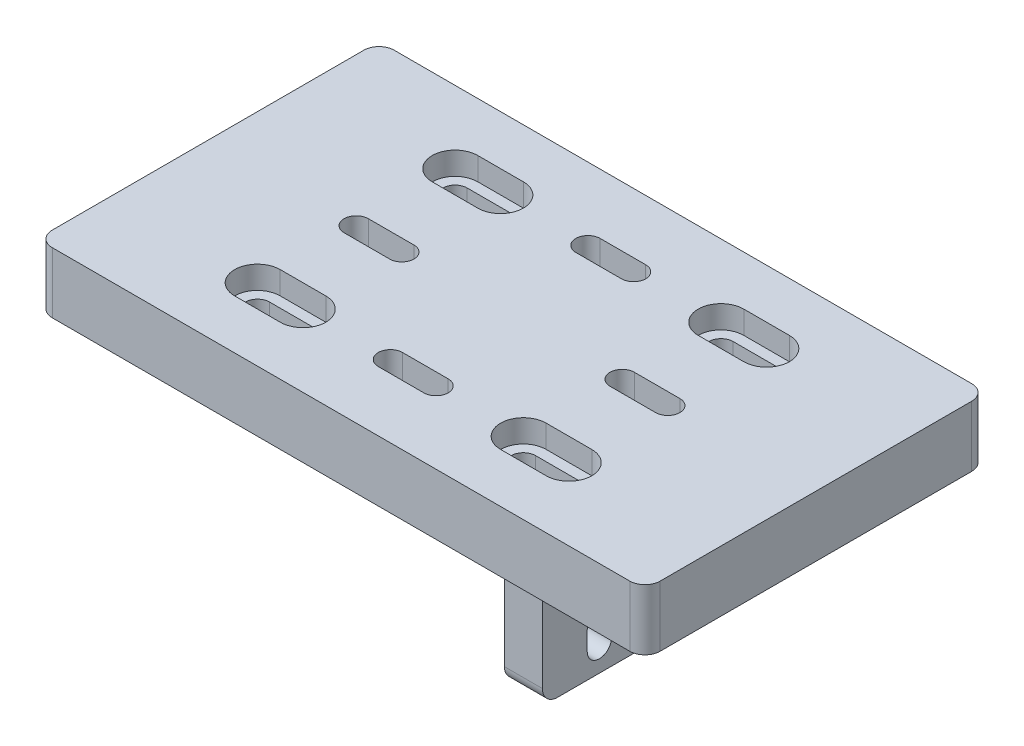
SolidWorks part; units mm, degrees
ref_plane "Alzado" through (0, 0, 0) normal (0, 0, 1) x (1, 0, 0)
ref_plane "Planta" through (0, 0, 0) normal (0, 1, 0) x (1, 0, 0)
ref_plane "Vista lateral" through (0, 0, 0) normal (1, 0, 0) x (0, 0, -1)
sketch "Croquis2" plane through (0, 0, 0) normal (0, 1, 0) x (1, 0, 0)
  line L0 (0, 22.5) -> (0, -22.5) construction
  line L1 (-40, -22.5) -> (40, -22.5)
  line L2 (-40, -22.5) -> (-40, 22.5)
  line L3 (-40, 22.5) -> (40, 22.5)
  line L4 (40, -22.5) -> (40, 22.5)
  line L5 (-40, -22.5) -> (40, 22.5) construction
  line L6 (-40, 22.5) -> (40, -22.5) construction
  line L7 (-30, 22.5) -> (-30, -22.5) construction
  line L8 (30, 22.5) -> (30, -22.5) construction
  line L9 (-20.5, 13) -> (-14.5, 13) construction
  line L10 (-20.5, 14.6) -> (-14.5, 14.6)
  line L11 (-20.5, 11.4) -> (-14.5, 11.4)
  line L12 (0, 0) -> (-40, 0) construction
  line L13 (20.5, 13) -> (14.5, 13) construction
  line L14 (20.5, 14.6) -> (14.5, 14.6)
  line L15 (20.5, 11.4) -> (14.5, 11.4)
  line L16 (20.5, -13) -> (14.5, -13) construction
  line L17 (20.5, -14.6) -> (14.5, -14.6)
  line L18 (20.5, -11.4) -> (14.5, -11.4)
  line L19 (-20.5, -13) -> (-14.5, -13) construction
  line L20 (-20.5, -14.6) -> (-14.5, -14.6)
  line L21 (-20.5, -11.4) -> (-14.5, -11.4)
  line L22 (-20.5, 0) -> (-14.5, 0) construction
  line L23 (-20.5, 1.6) -> (-14.5, 1.6)
  line L24 (-20.5, -1.6) -> (-14.5, -1.6)
  line L25 (20.5, 0) -> (14.5, 0) construction
  line L26 (20.5, 1.6) -> (14.5, 1.6)
  line L27 (20.5, -1.6) -> (14.5, -1.6)
  line L28 (-17.5, 13) -> (-17.5, -13) construction
  line L29 (17.5, 13) -> (17.5, -13) construction
  line L30 (-3, 13) -> (3, 13) construction
  line L31 (-3, 14.6) -> (3, 14.6)
  line L32 (-3, 11.4) -> (3, 11.4)
  line L33 (-3, -13) -> (3, -13) construction
  line L34 (-3, -11.4) -> (3, -11.4)
  line L35 (-3, -14.6) -> (3, -14.6)
  arc A0 (-20.5, 14.6) -> (-20.5, 11.4) centre (-20.5, 13) ccw
  arc A1 (-14.5, 11.4) -> (-14.5, 14.6) centre (-14.5, 13) ccw
  arc A2 (20.5, 14.6) -> (20.5, 11.4) centre (20.5, 13) cw
  arc A3 (14.5, 11.4) -> (14.5, 14.6) centre (14.5, 13) cw
  arc A4 (20.5, -14.6) -> (20.5, -11.4) centre (20.5, -13) ccw
  arc A5 (14.5, -11.4) -> (14.5, -14.6) centre (14.5, -13) ccw
  arc A6 (-20.5, -14.6) -> (-20.5, -11.4) centre (-20.5, -13) cw
  arc A7 (-14.5, -11.4) -> (-14.5, -14.6) centre (-14.5, -13) cw
  arc A8 (-20.5, 1.6) -> (-20.5, -1.6) centre (-20.5, 0) ccw
  arc A9 (-14.5, -1.6) -> (-14.5, 1.6) centre (-14.5, 0) ccw
  arc A10 (20.5, 1.6) -> (20.5, -1.6) centre (20.5, 0) cw
  arc A11 (14.5, -1.6) -> (14.5, 1.6) centre (14.5, 0) cw
  arc A12 (-3, 14.6) -> (-3, 11.4) centre (-3, 13) ccw
  arc A13 (3, 11.4) -> (3, 14.6) centre (3, 13) ccw
  arc A14 (-3, -11.4) -> (-3, -14.6) centre (-3, -13) ccw
  arc A15 (3, -14.6) -> (3, -11.4) centre (3, -13) ccw
  point P0 (0, 0)
  point P14 (-17.5, 13)
  point P23 (17.5, 13)
  point P30 (17.5, -13)
  point P37 (-17.5, -13)
  point P44 (-17.5, 0)
  point P53 (17.5, 0)
  point P62 (0, 13)
  point P69 (0, -13)
  dimension "D5" = 1.6
  dimension "D9" = 1.6
  dimension "D1" = 45
  dimension "D2" = 80
  dimension "D3" = 60
  dimension "D4" = 30
  dimension "D6" = 13
  dimension "D7" = 12.5
  dimension "D8" = 6
  dimension "D10" = 6
extrude "Saliente-Extruir1" add sketch "Croquis2" along normal blind 8
sketch "Croquis3" plane through (0, 8, 0) normal (0, 1, 0) x (1, 0, 0)
  line L0 (0, 22.5) -> (0, -22.5) construction
  line L1 (40, 22.5) -> (-40, 22.5) construction
  line L2 (-40, -22.5) -> (40, -22.5) construction
  line L3 (-40, 0) -> (40, 0) construction
  line L4 (-40, 22.5) -> (-40, -22.5) construction
  line L5 (40, -22.5) -> (40, 22.5) construction
  line L6 (-17.5, 14.6) -> (-17.5, 11.4) construction
  line L7 (-14.5, 14.6) -> (-20.5, 14.6) construction
  line L8 (-20.5, 11.4) -> (-14.5, 11.4) construction
  line L9 (-20.5, 13) -> (-14.5, 13) construction
  line L10 (-20.5, 16) -> (-14.5, 16)
  line L11 (-20.5, 10) -> (-14.5, 10)
  line L12 (20.5, 13) -> (14.5, 13) construction
  line L13 (20.5, 16) -> (14.5, 16)
  line L14 (20.5, 10) -> (14.5, 10)
  line L15 (20.5, -13) -> (14.5, -13) construction
  line L16 (20.5, -16) -> (14.5, -16)
  line L17 (20.5, -10) -> (14.5, -10)
  line L18 (-20.5, -13) -> (-14.5, -13) construction
  line L19 (-20.5, -16) -> (-14.5, -16)
  line L20 (-20.5, -10) -> (-14.5, -10)
  arc A0 (-20.5, 16) -> (-20.5, 10) centre (-20.5, 13) ccw
  arc A1 (-14.5, 10) -> (-14.5, 16) centre (-14.5, 13) ccw
  arc A2 (20.5, 16) -> (20.5, 10) centre (20.5, 13) cw
  arc A3 (14.5, 10) -> (14.5, 16) centre (14.5, 13) cw
  arc A4 (20.5, -16) -> (20.5, -10) centre (20.5, -13) ccw
  arc A5 (14.5, -10) -> (14.5, -16) centre (14.5, -13) ccw
  arc A6 (-20.5, -16) -> (-20.5, -10) centre (-20.5, -13) cw
  arc A7 (-14.5, -10) -> (-14.5, -16) centre (-14.5, -13) cw
  point P20 (-17.5, 13)
  point P28 (17.5, 13)
  point P35 (17.5, -13)
  point P42 (-17.5, -13)
  dimension "D1" = 3
extrude "Cortar-Extruir1" cut sketch "Croquis3" against normal blind 3
sketch "Croquis4" plane through (0, 0, 0) normal (0, -1, 0) x (1, 0, 0)
  line L0 (0, 22.5) -> (0, -22.5) construction
  line L1 (-40, 22.5) -> (40, 22.5) construction
  line L2 (40, -22.5) -> (-40, -22.5) construction
  line L3 (6.5, 22.5) -> (6.5, -22.5) construction
  line L4 (6.5, 7.5) -> (6.5, -7.5)
  line L5 (0, 0) -> (13, 0) construction
  line L6 (6.5, 7.5) -> (11.5, 7.5)
  line L8 (11.5, -7.5) -> (6.5, -7.5)
  line L9 (11.5, -7.5) -> (11.5, 7.5)
  point P14 (6.5, 0)
  dimension "D1" = 6.5
  dimension "D2" = 15
  dimension "D4" = 5
extrude "Saliente-Extruir2" add sketch "Croquis4" along normal blind 35
sketch "Croquis5" plane through (6.5, 0, 0) normal (-1, 0, 0) x (0, 0, 1)
  line L0 (0, 0) -> (0, -35) construction
  line L1 (7.5, 0) -> (-7.5, 0) construction
  line L2 (7.5, -35) -> (-7.5, -35) construction
  line L3 (0, -17.5) -> (7.5, -17.5) construction
  line L4 (7.5, -35) -> (7.5, 0) construction
  line L5 (0, -11.25) -> (0, -13.75) construction
  line L6 (1.6, -11.25) -> (1.6, -13.75)
  line L7 (-1.6, -11.25) -> (-1.6, -13.75)
  line L8 (0, -23.75) -> (0, -21.25) construction
  line L9 (1.6, -23.75) -> (1.6, -21.25)
  line L10 (-1.6, -23.75) -> (-1.6, -21.25)
  circle A0 centre (0, -12.5) radius 1.6 construction
  circle A1 centre (0, -22.5) radius 1.6 construction
  arc A2 (1.6, -11.25) -> (-1.6, -11.25) centre (0, -11.25) ccw
  arc A3 (-1.6, -13.75) -> (1.6, -13.75) centre (0, -13.75) ccw
  arc A4 (1.6, -23.75) -> (-1.6, -23.75) centre (0, -23.75) cw
  arc A5 (-1.6, -21.25) -> (1.6, -21.25) centre (0, -21.25) cw
  point P16 (0, -12.5)
  point P23 (0, -22.5)
  dimension "D1" = 3.2
  dimension "D3" = 1.6
  dimension "D2" = 5
  dimension "D4" = 2.5
extrude "Cortar-Extruir2" cut sketch "Croquis5" against normal through all
fillet "Redondeo1" radius 5 2 edges at (9, 0, 7.5) (9, 0, -7.5)
sketch "Croquis6" plane through (0, 0, 0) normal (0, -1, 0) x (1, 0, 0)
  line L0 (0, 0) -> (-40, 0) construction
  line L1 (-22.5, 2.8) -> (-12.5, 2.8)
  line L2 (-22.5, 2.8) -> (-22.5, -2.8)
  line L3 (-22.5, -2.8) -> (-12.5, -2.8)
  line L4 (-12.5, 2.8) -> (-12.5, -2.8)
  line L5 (-22.5, 2.8) -> (-12.5, -2.8) construction
  line L6 (-22.5, -2.8) -> (-12.5, 2.8) construction
  line L7 (-40, -22.5) -> (-40, 22.5) construction
  line L8 (0, 0) -> (0, 6.822) construction
  line L10 (22.5, -2.8) -> (12.5, -2.8)
  line L11 (12.5, 2.8) -> (12.5, -2.8)
  line L12 (22.5, 2.8) -> (12.5, 2.8)
  line L13 (22.5, 2.8) -> (22.5, -2.8)
  line L14 (0, 14.6) -> (0, 11.4) construction
  line L15 (-3, 14.6) -> (3, 14.6) construction
  line L16 (3, 11.4) -> (-3, 11.4) construction
  line L17 (0, -11.4) -> (0, -14.6) construction
  line L18 (-5, 15.8) -> (5, 15.8)
  line L19 (-5, 15.8) -> (-5, 10.2)
  line L20 (-5, 10.2) -> (5, 10.2)
  line L21 (5, 15.8) -> (5, 10.2)
  line L22 (-5, 15.8) -> (5, 10.2) construction
  line L23 (-5, 10.2) -> (5, 15.8) construction
  line L24 (-3, -11.4) -> (3, -11.4) construction
  line L25 (3, -14.6) -> (-3, -14.6) construction
  line L27 (-5, -15.8) -> (5, -15.8)
  line L28 (-5, -15.8) -> (-5, -10.2)
  line L29 (-5, -10.2) -> (5, -10.2)
  line L30 (5, -15.8) -> (5, -10.2)
  line L31 (-5, -15.8) -> (5, -10.2) construction
  line L32 (-5, -10.2) -> (5, -15.8) construction
  point P0 (-17.5, 0)
  point P12 (0, -13)
  point P21 (0, 13)
  dimension "D1" = 5.6
  dimension "D2" = 10
  dimension "D3" = 17.5
extrude "Cortar-Extruir3" cut sketch "Croquis6" against normal blind 3
sketch "Croquis8" plane through (6.5, 0, 0) normal (-1, 0, 0) x (0, 0, 1)
  line L0 (0, -12.5) -> (0, -22.5) construction
  line L1 (0, -17.5) -> (7.5, -17.5) construction
  line L2 (7.5, -35) -> (7.5, -5) construction
  line L4 (0, 0) -> (12.5, 0) construction
  line L5 (12.5, 0) -> (-12.5, 0) construction
  line L6 (-7.5, -27) -> (7.5, -27)
  line L7 (-7.5, -35) -> (-7.5, -5) construction
  line L8 (7.5, -35) -> (7.5, -5) construction
  line L9 (-7.5, -27) -> (-7.5, -35)
  line L10 (-7.5, -35) -> (7.5, -35)
  line L11 (7.5, -35) -> (7.5, -27)
  line L12 (1.6, -12.5) -> (0, -12.5) construction
  line L13 (1.6, -13.75) -> (1.6, -11.25) construction
  line L14 (1.6, -22.5) -> (0, -22.5) construction
  line L15 (1.6, -23.75) -> (1.6, -21.25) construction
  dimension "D2" = 7.5
  dimension "D1" = 27
extrude "Cortar-Extruir4" cut sketch "Croquis8" against normal through all
fillet "Redondeo2" radius 2 6 edges at (40, 4, 22.5) (40, 4, -22.5) (9, -27, 7.5) (9, -27, -7.5) (-40, 4, 22.5) (-40, 4, -22.5)
sketch "Croquis10" plane through (11.5, 0, 0) normal (1, 0, 0) x (0, 0, -1)
  line L0 (0, -12.5) -> (0, -22.5) construction
  line L1 (0, -17.5) -> (3.2732, -17.5) construction
  line L2 (1.6, -12.5) -> (0, -12.5) construction
  line L3 (1.6, -11.25) -> (1.6, -13.75) construction
  line L4 (1.6, -22.5) -> (0, -22.5) construction
  line L5 (1.6, -21.25) -> (1.6, -23.75) construction
  dimension "D1" = 17.5
